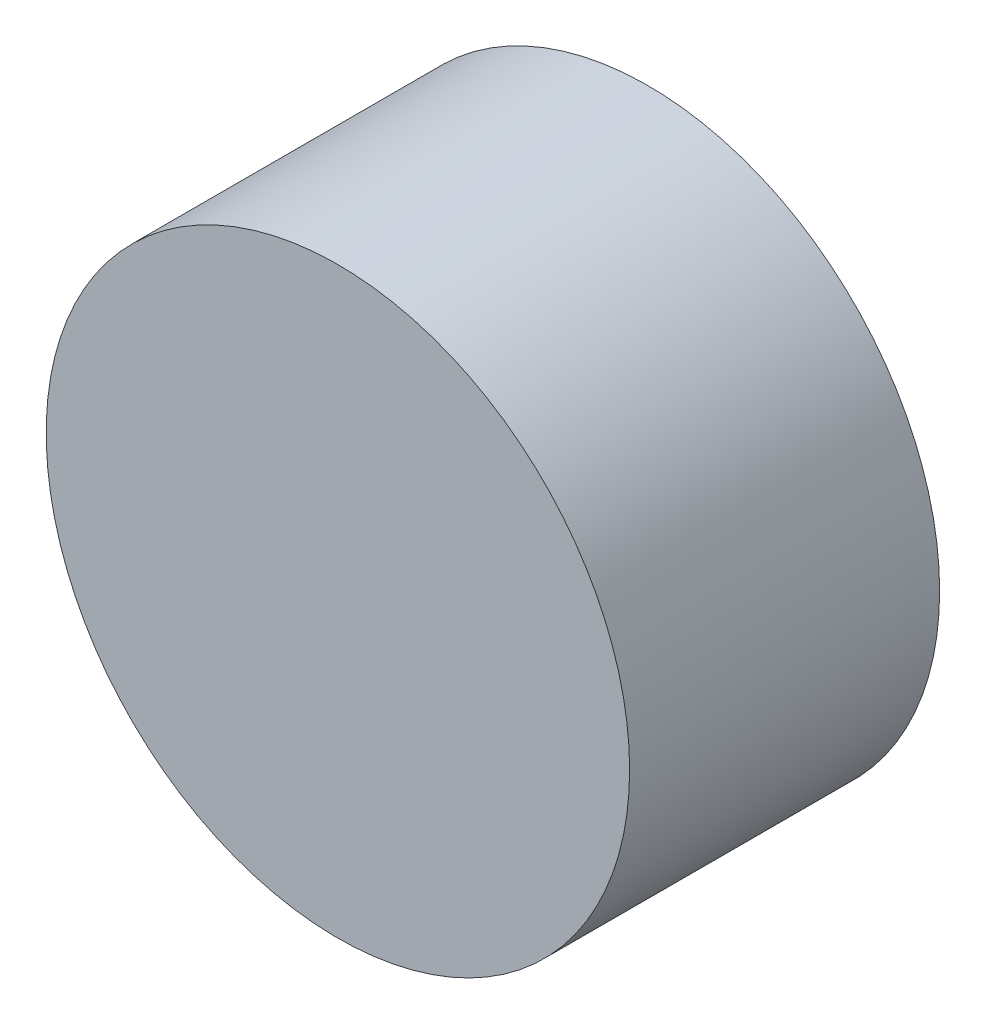
SolidWorks part; units mm, degrees
ref_plane "Front Plane" through (0, 0, 0) normal (0, 0, 1) x (1, 0, 0)
ref_plane "Top Plane" through (0, 0, 0) normal (0, 1, 0) x (1, 0, 0)
ref_plane "Right Plane" through (0, 0, 0) normal (1, 0, 0) x (0, 0, -1)
sketch "Sketch1" plane through (0, 0, 0) normal (0, 0, 1) x (1, 0, 0)
  circle A0 centre (0, 0) radius 9.41
  dimension "D1" = 18.82
extrude "Boss-Extrude1" add sketch "Sketch1" along normal blind 10
sketch "Sketch2" plane through (0, 0, 10) normal (0, 0, 1) x (1, 0, 0)
  point P0 (0, 0)
sketch "Sketch3" plane through (0, 0, 0) normal (0, 0, -1) x (-1, 0, 0)
  line L0 (0, 0) -> (0, 9.41) construction
  line L2 (9.41, 0) -> (0, 0) construction
  line L3 (0, 0) -> (0, -9.41) construction
  line L5 (-9.41, 0) -> (0, 0) construction
  circle A0 centre (0, 0) radius 9.41 construction
sketch "Sketch4" plane through (0, 0, 10) normal (0, 0, 1) x (1, 0, 0)
  line L0 (0, 0) -> (-9.41, 0) construction
  line L2 (0, 9.41) -> (0, 0) construction
  line L3 (0, 0) -> (0, -9.41) construction
  line L5 (9.41, 0) -> (0, 0) construction
  circle A0 centre (0, 0) radius 9.41 construction
